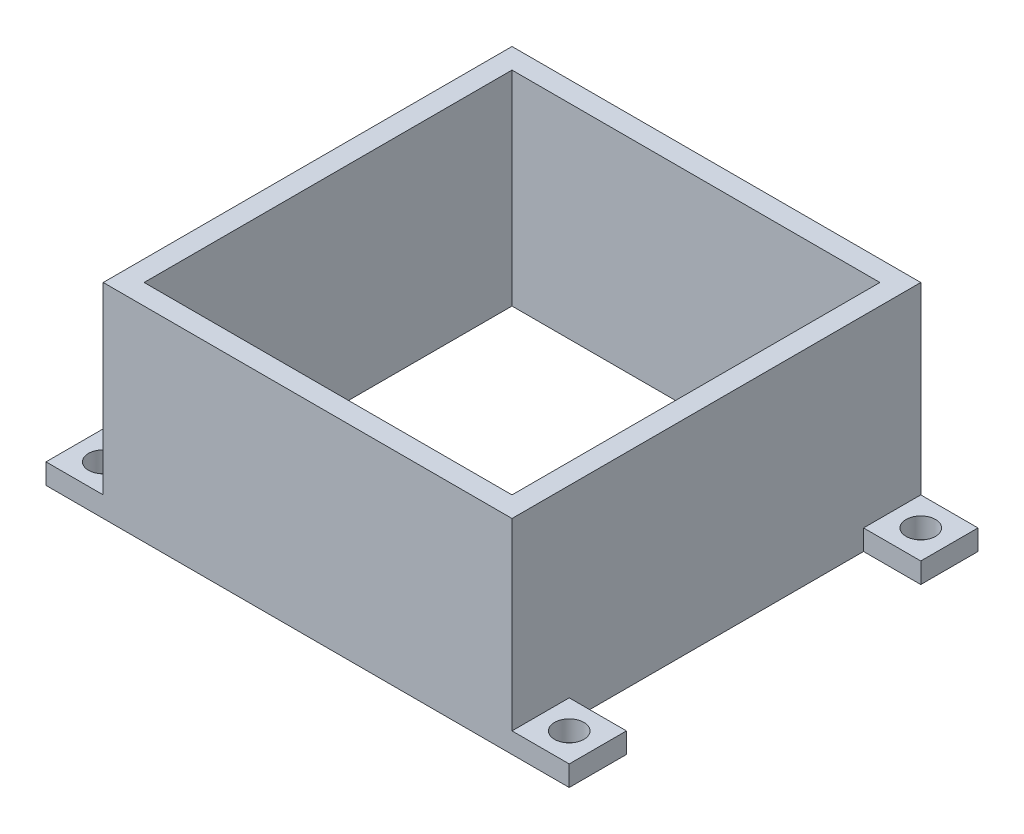
SolidWorks part; units mm, degrees
ref_plane "Ebene vorne" through (0, 0, 0) normal (0, 0, 1) x (1, 0, 0)
ref_plane "Ebene oben" through (0, 0, 0) normal (0, 1, 0) x (1, 0, 0)
ref_plane "Ebene rechts" through (0, 0, 0) normal (1, 0, 0) x (0, 0, -1)
sketch "Skizze1" plane through (0, 0, 0) normal (0, 1, 0) x (1, 0, 0)
  line L0 (-22.5, 22.5) -> (22.5, 22.5)
  line L1 (-25, 25) -> (25, 25)
  line L2 (-25, 25) -> (-25, -25)
  line L3 (-25, -25) -> (25, -25)
  line L4 (25, 25) -> (25, -25)
  line L5 (22.5, 22.5) -> (22.5, -22.5)
  line L6 (-22.5, -22.5) -> (22.5, -22.5)
  line L7 (-22.5, 22.5) -> (-22.5, -22.5)
  point P4 (0, 25)
  point P6 (25, 0)
  dimension "D1" = 50
  dimension "D2" = 50
  dimension "D3" = 2.5
extrude "Aufsatz-Linear austragen1" add sketch "Skizze1" along normal blind 25
sketch "Skizze2" plane through (0, 0, 0) normal (0, -1, 0) x (1, 0, 0)
  line L1 (-25, 25) -> (-32, 25)
  line L2 (-25, 25) -> (-25, 18)
  line L3 (-25, 18) -> (-32, 18)
  line L4 (-32, 25) -> (-32, 18)
  circle A0 centre (-28.5, 21.5) radius 1.8
  point P7 (0, 0)
  point P8 (-28.5, 25)
  point P9 (0, 0)
  point P10 (-32, 21.5)
  dimension "D1" = 7
  dimension "D2" = 7
extrude "Aufsatz-Linear austragen2" add sketch "Skizze2" against normal blind 2.5
mirror "Spiegeln1" about plane through (0, 0, 0) normal (1, 0, 0) of "Aufsatz-Linear austragen2"
mirror "Spiegeln2" about plane through (0, 0, 0) normal (0, 0, 1) of "Spiegeln1", "Aufsatz-Linear austragen2"
